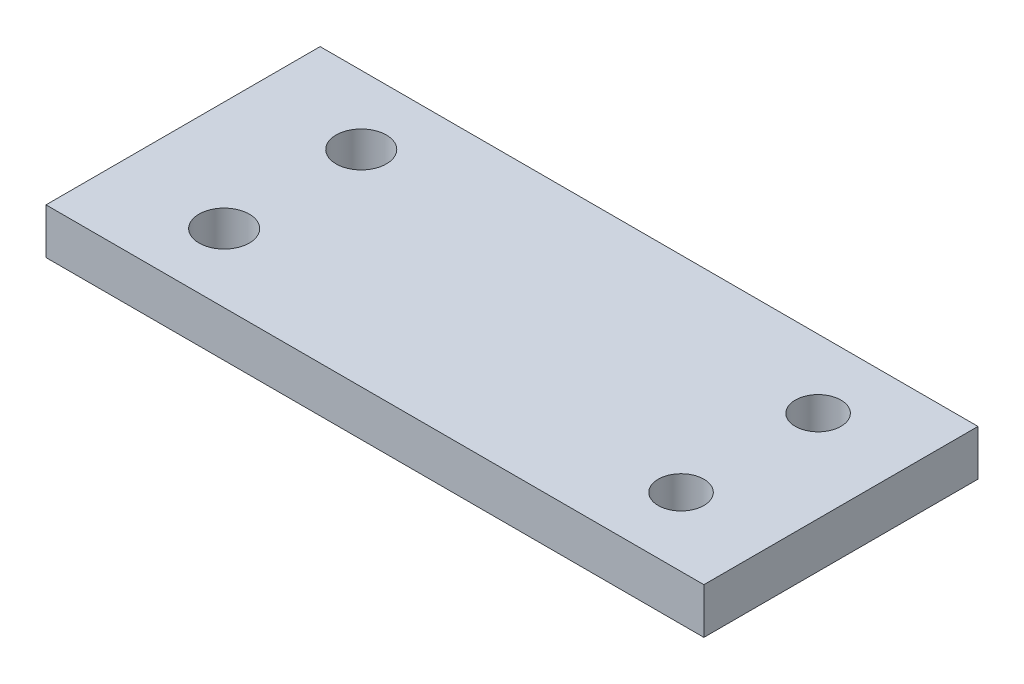
SolidWorks part; units mm, degrees
ref_plane "Front Plane" through (0, 0, 0) normal (0, 0, 1) x (1, 0, 0)
ref_plane "Top Plane" through (0, 0, 0) normal (0, 1, 0) x (1, 0, 0)
ref_plane "Right Plane" through (0, 0, 0) normal (1, 0, 0) x (0, 0, -1)
sketch "Sketch1" plane through (0, 0, 0) normal (0, 1, 0) x (1, 0, 0)
  line L1 (-36, 15) -> (36, 15)
  line L2 (-36, 15) -> (-36, -15)
  line L3 (-36, -15) -> (36, -15)
  line L4 (36, 15) -> (36, -15)
  line L5 (-36, 15) -> (36, -15) construction
  line L6 (-36, -15) -> (36, 15) construction
  point P0 (0, 0)
  dimension "D1" = 72
  dimension "D2" = 30
extrude "Boss-Extrude1" add sketch "Sketch1" along normal blind 5
sketch "Sketch3" plane through (0, 5, 0) normal (0, 1, 0) x (1, 0, 0)
  line L0 (36, 15) -> (-36, 15) construction
  line L1 (-36, 15) -> (-36, -15) construction
  line L2 (36, -15) -> (36, 15) construction
  circle A0 centre (-24, 7.5) radius 2.75
  circle A1 centre (-24, -7.5) radius 2.75
  circle A2 centre (26, 7.5) radius 2.5
  circle A3 centre (26, -7.5) radius 2.5
  dimension "D1" = 5.5
  dimension "D2" = 5.5
  dimension "D6" = 5
  dimension "D7" = 5
  dimension "D3" = 7.5
  dimension "D4" = 15
  dimension "D5" = 12
  dimension "D8" = 10
extrude "Cut-Extrude1" cut sketch "Sketch3" against normal through all
